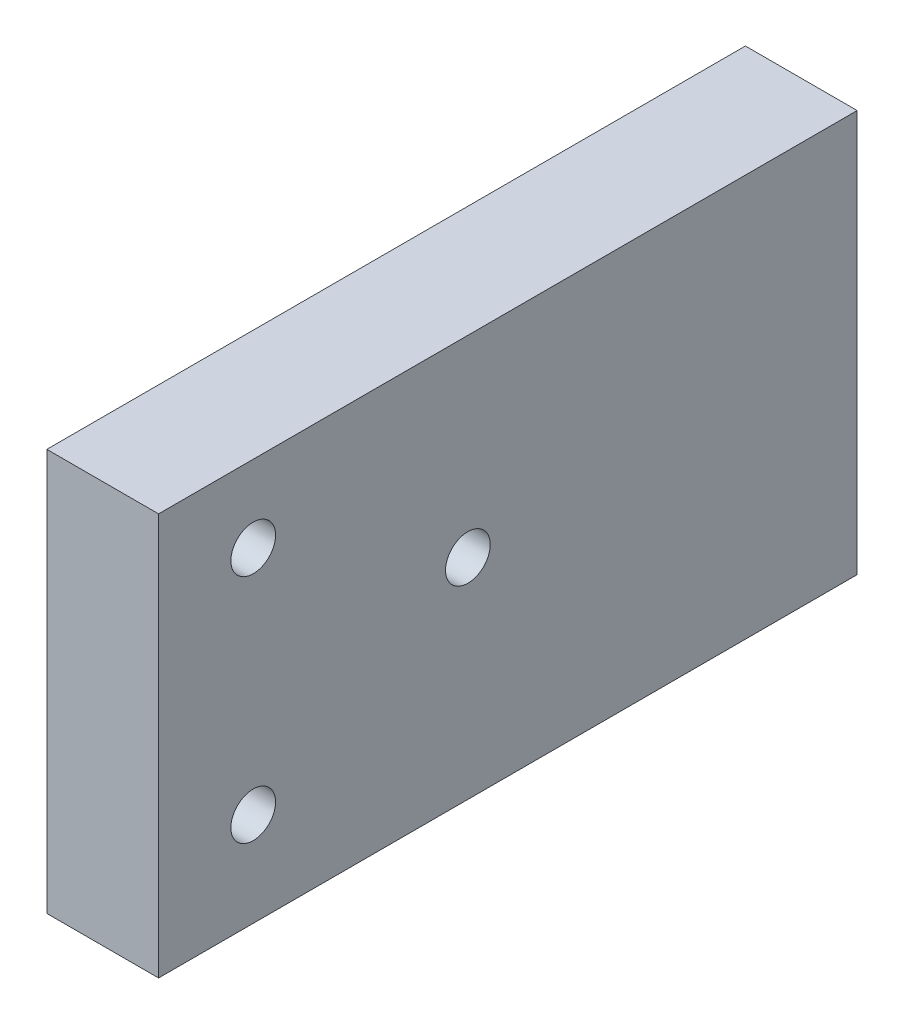
SolidWorks part; units mm, degrees
ref_plane "Alzado" through (0, 0, 0) normal (0, 0, 1) x (1, 0, 0)
ref_plane "Planta" through (0, 0, 0) normal (0, 1, 0) x (1, 0, 0)
ref_plane "Vista lateral" through (0, 0, 0) normal (1, 0, 0) x (0, 0, -1)
sketch "Croquis1" plane through (0, 0, 0) normal (0, 0, 1) x (1, 0, 0)
  line L1 (94, -5) -> (86, -5)
  line L2 (94, -5) -> (94, 23.7685)
  line L3 (94, 23.7685) -> (86, 23.7685)
  line L4 (86, -5) -> (86, 23.7685)
  dimension "D1" = 8
  dimension "D3" = 28.7685
extrude "Saliente-Extruir1" add sketch "Croquis1" along normal blind 50
sketch "Croquis3" plane through (86, 0, 0) normal (1, 0, 0) x (0, 0, -1)
  line L0 (0, -5) -> (-55.727, -5) construction
  line L1 (-99, -5) -> (0, -5) construction
  line L2 (-55.727, -5) -> (-55.727, 25) construction
  line L3 (-99, 25) -> (0, 25) construction
  line L4 (-55.727, 25) -> (0, 25) construction
  line L5 (0, 25) -> (0, -5) construction
  line L7 (-55.727, 25) -> (0, -5) construction
  line L8 (-55.727, 25) -> (0, 25) construction
  line L9 (-55.727, -5) -> (0, -5) construction
  line L10 (0, 25) -> (0, -5) construction
  line L11 (0, 25) -> (-55.727, -5) construction
  circle A0 centre (-43.227, 1.7292) radius 1.6
  circle A1 centre (-27.8635, 10) radius 1.6
  circle A4 centre (-43.227, 18.2708) radius 1.6
  point P21 (-27.8635, 10)
  dimension "D1" = 3.2
  dimension "D3" = 12.5
extrude "Cortar-Extruir1" cut sketch "Croquis3" along normal up to next
sketch "Croquis4" plane through (0, 0, 0) normal (0, 0, -1) x (-1, 0, 0)
  line L0 (-94, -5) -> (-94, 23.7685) construction
  line L1 (-100, -5) -> (-86, -5) construction
  line L2 (-100, -5) -> (-100, 23.7685) construction
  line L3 (-100, 23.7685) -> (-86, 23.7685) construction
  line L4 (-86, -5) -> (-86, 23.7685) construction
  line L5 (-90, 23.7685) -> (-90, -5) construction
  line L6 (-94, 9.3842) -> (-86, 9.3842) construction
  line L7 (-94, 23.7685) -> (-86, 23.7685) construction
  circle A0 centre (-90.0736, 1) radius 1.95
  circle A1 centre (-90, 9.3842) radius 1.95
  circle A2 centre (-90, 17.7685) radius 1.95
  point P20 (-90, 9.3842)
  dimension "D2" = 3.9
  dimension "D1" = 14
  dimension "D3" = 4
  dimension "D5" = 6
  dimension "D7" = 6
extrude "Cortar-Extruir2" cut sketch "Croquis4" against normal blind 22
